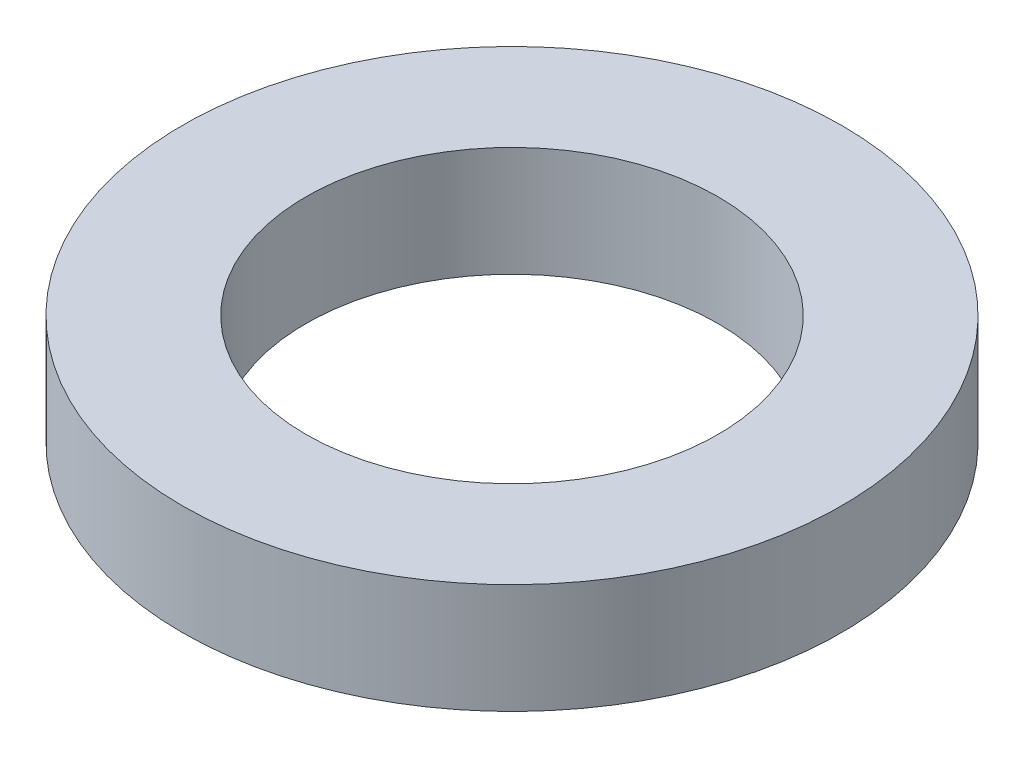
SolidWorks part; units mm, degrees
ref_plane "Front Plane" through (0, 0, 0) normal (0, 0, 1) x (1, 0, 0)
ref_plane "Top Plane" through (0, 0, 0) normal (0, 1, 0) x (1, 0, 0)
ref_plane "Right Plane" through (0, 0, 0) normal (1, 0, 0) x (0, 0, -1)
sketch "Sketch1" plane through (0, 0, 0) normal (0, 1, 0) x (1, 0, 0)
  circle A0 centre (0, 0) radius 3.75
  circle A1 centre (0, 0) radius 6
  dimension "D1" = 7.5
  dimension "D2" = 12
extrude "Boss-Extrude1" add sketch "Sketch1" along normal blind 2
